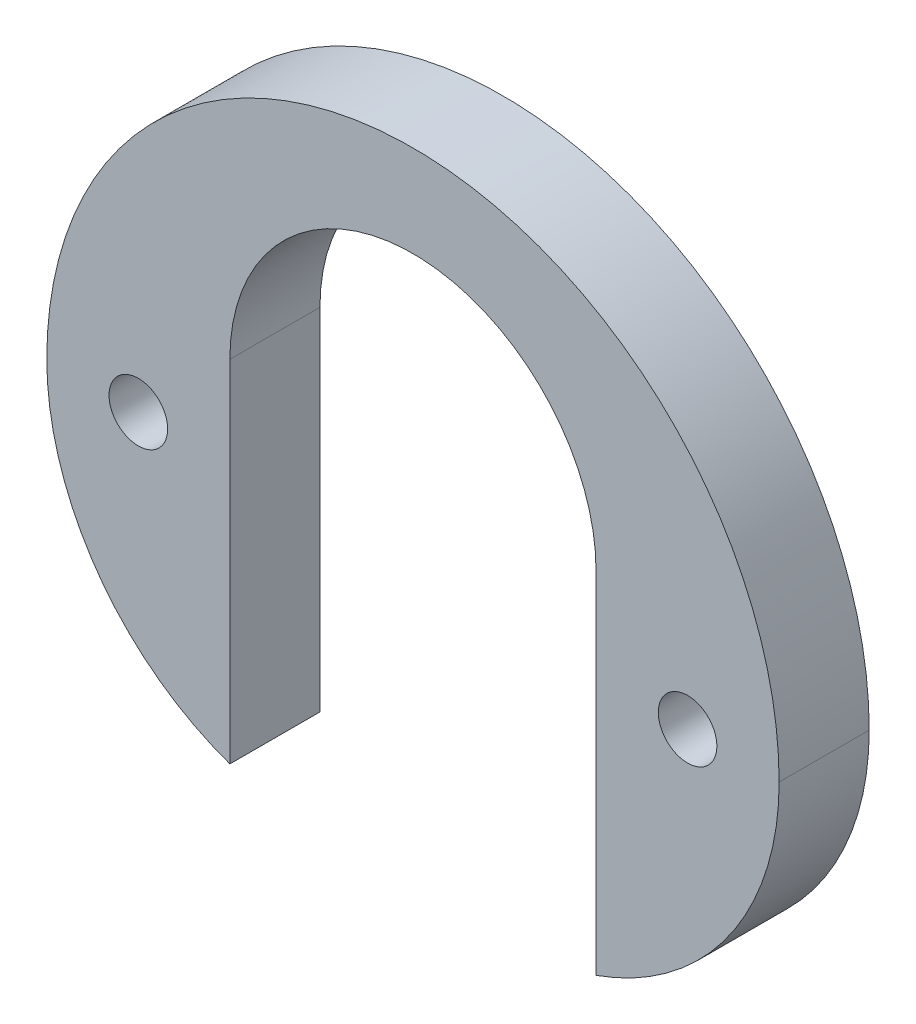
SolidWorks part; units mm, degrees
ref_plane "Alzado" through (0, 0, 0) normal (0, 0, 1) x (1, 0, 0)
ref_plane "Planta" through (0, 0, 0) normal (0, 1, 0) x (1, 0, 0)
ref_plane "Vista lateral" through (0, 0, 0) normal (1, 0, 0) x (0, 0, -1)
sketch "Croquis1" plane through (0, 0, 0) normal (0, 0, 1) x (1, 0, 0)
  line L0 (0, 3.175) -> (0, -3.175) construction
  line L1 (-3.175, 0) -> (3.175, 0) construction
  line L2 (-3.175, 9.525) -> (3.175, 9.525)
  line L3 (-3.175, -9.525) -> (3.175, -9.525)
  line L6 (0, 3.175) -> (0, -3.175) construction
  line L7 (6.35, 3.175) -> (6.35, -3.175)
  line L8 (-6.35, 3.175) -> (-6.35, -3.175)
  line L9 (6.35, -3.175) -> (6.35, -8.9803)
  line L10 (-6.35, -3.175) -> (-6.35, -8.9803)
  circle A0 centre (0, 3.175) radius 6.35
  circle A1 centre (0, -3.175) radius 6.35
  arc A3 (-3.175, 9.525) -> (-3.175, -9.525) centre (-3.175, 0) ccw
  arc A4 (3.175, -9.525) -> (3.175, 9.525) centre (3.175, 0) ccw
  arc A5 (-12.7, 0) -> (0, 12.7) centre (0, 0) cw
  arc A7 (0, 12.7) -> (12.7, 0) centre (0, 0) cw
  arc A8 (6.35, 3.175) -> (-6.35, 3.175) centre (0, 3.175) ccw
  arc A9 (-6.35, -3.175) -> (6.35, -3.175) centre (0, -3.175) ccw
  circle A10 centre (-9.525, 0) radius 1.016
  circle A11 centre (9.525, 0) radius 1.016
  circle A12 centre (9.525, 0) radius 1.016
  point P7 (0, 0)
  point P12 (0, 0)
  dimension "D1" = 9.525
  dimension "D2" = 2.032
  dimension "D3" = 6.35
  dimension "D4" = 12.7
  dimension "D5" = 12.7
  dimension "D6" = 3.175
  dimension "D7" = 3.175
extrude "Saliente-Extruir1" add sketch "Croquis1" along normal blind 3.1242 contours L2 A3 L10 L8 A0 A10 | A7 A5 A3 L2 A4 | L9 A4 L2 A0 L7 A11
